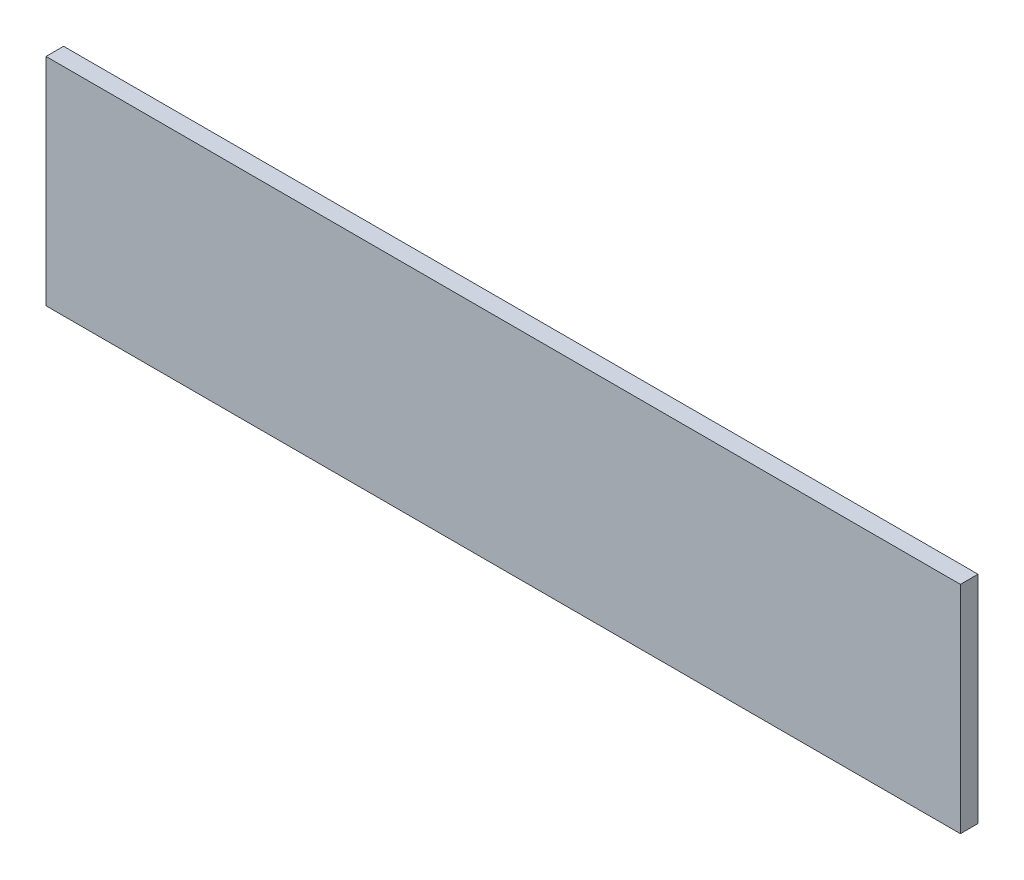
SolidWorks part; units mm, degrees
ref_plane "Alzado" through (0, 0, 0) normal (0, 0, 1) x (1, 0, 0)
ref_plane "Planta" through (0, 0, 0) normal (0, 1, 0) x (1, 0, 0)
ref_plane "Vista lateral" through (0, 0, 0) normal (1, 0, 0) x (0, 0, -1)
sketch "Croquis1" plane through (0, 0, 0) normal (0, 0, 1) x (1, 0, 0)
  line L0 (-125.1847, 27.9518) -> (124.8153, 27.9518) construction
  line L1 (-125.1847, 27.9518) -> (-125.1847, -28.4551) construction
  line L2 (-125.1847, -28.4551) -> (124.8153, -28.4551) construction
  line L3 (124.8153, 27.9518) -> (124.8153, -28.4551) construction
  line L5 (129.8153, 27.9518) -> (129.8153, -33.4551)
  line L6 (-130.1847, -33.4551) -> (129.8153, -33.4551)
  line L7 (-130.1847, 27.9518) -> (-130.1847, -33.4551)
  line L8 (-130.1847, 32.9518) -> (129.8153, 32.9518) construction
  line L9 (-130.1847, 27.9518) -> (129.8153, 27.9518)
  line L10 (-125.1847, -5.2516) -> (-75.1847, -5.2516) construction
  line L11 (-130.1847, 32.9518) -> (-130.1847, -33.4551) construction
  line L12 (129.8153, 32.9518) -> (129.8153, -33.4551) construction
  line L13 (-75.1847, -5.2516) -> (-25.1847, -5.2516) construction
  line L14 (-25.1847, -5.2516) -> (24.8153, -5.2516) construction
  line L15 (24.8153, -5.2516) -> (74.8153, -5.2516) construction
  line L16 (74.8153, -5.2516) -> (124.8153, -5.2516) construction
  line L17 (-0.1847, 27.9518) -> (-0.1847, -5.2516) construction
  circle A0 centre (-75.1847, -5.2516) radius 15.5 construction
  circle A1 centre (74.8153, -5.2516) radius 15.5 construction
  circle A2 centre (24.8153, -5.2516) radius 12.5 construction
  circle A3 centre (-25.1847, -5.2516) radius 12.5 construction
  dimension "D2" = 31
  dimension "D3" = 25
  dimension "D4" = 260
  dimension "D5" = 61.4069
  dimension "D6" = 33.2035
  dimension "D1" = 5
extrude "Saliente-Extruir1" add sketch "Croquis1" along normal blind 5
sketch "Croquis2" [suppressed] plane through (0, 0, 5) normal (0, 0, 1) x (1, 0, 0)
  circle A0 centre (-25.1847, -5.2516) radius 12.5
  circle A1 centre (24.8153, -5.2516) radius 12.5
extrude "Cortar-Extruir1" [suppressed] cut sketch "Croquis2" against normal up to next
sketch "Croquis3" [suppressed] plane through (0, 0, 5) normal (0, 0, 1) x (1, 0, 0)
  circle A0 centre (-75.1847, -5.2516) radius 15.5
  circle A1 centre (74.8153, -5.2516) radius 15.5
extrude "Cortar-Extruir2" [suppressed] cut sketch "Croquis3" against normal up to next
sketch "Croquis4" [suppressed] plane through (0, 0, 5) normal (0, 0, 1) x (1, 0, 0)
  circle A0 centre (-75.1847, -5.2516) radius 15.5
  circle A1 centre (-25.1847, -5.2516) radius 12.5
  circle A2 centre (24.8153, -5.2516) radius 12.5
  circle A3 centre (74.8153, -5.2516) radius 15.5
extrude "Cortar-Extruir3" [suppressed] cut sketch "Croquis4" against normal up to next
